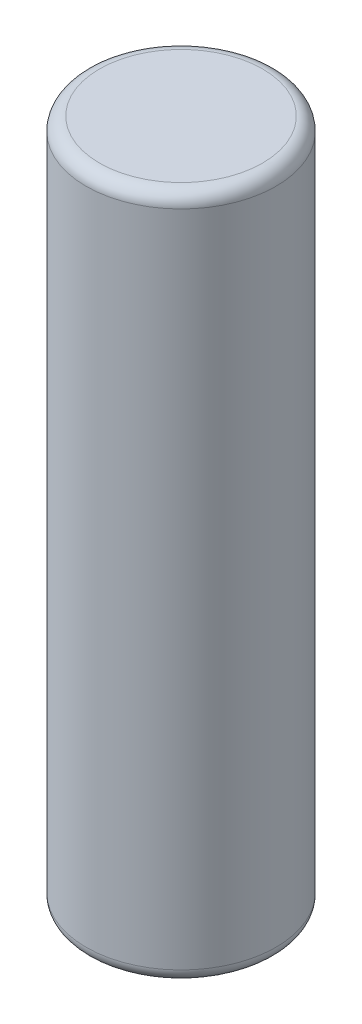
SolidWorks part; units mm, degrees
ref_plane "Front Plane" through (0, 0, 0) normal (0, 0, 1) x (1, 0, 0)
ref_plane "Top Plane" through (0, 0, 0) normal (0, 1, 0) x (1, 0, 0)
ref_plane "Right Plane" through (0, 0, 0) normal (1, 0, 0) x (0, 0, -1)
sketch "Sketch1" plane through (0, 0, 0) normal (0, 1, 0) x (1, 0, 0)
  circle A0 centre (0, 0) radius 9
  dimension "D1" = 18
extrude "Boss-Extrude1" add sketch "Sketch1" along normal blind 65
fillet "Fillet1" radius 1.27 2 edges at (0, 0, 9) (0, 65, 9)
